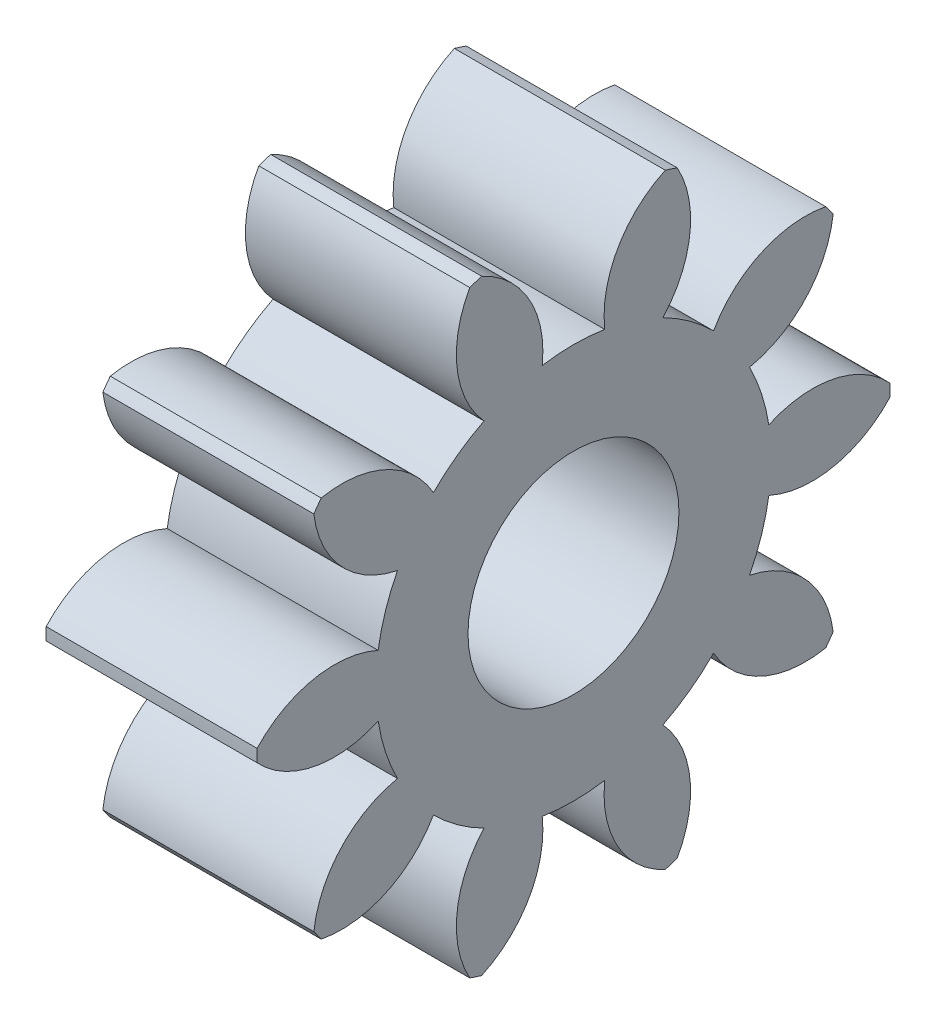
SolidWorks part; units mm, degrees
ref_plane "Plane1" through (0, 0, 0) normal (0, 0, 1) x (1, 0, 0)
ref_plane "Plane2" through (0, 0, 0) normal (0, 1, 0) x (1, 0, 0)
ref_plane "Plane3" through (0, 0, 0) normal (1, 0, 0) x (0, 0, -1)
other "Configuration Table"
sketch "HoldingSke" plane through (0, 0, 0) normal (0, 1, 0) x (1, 0, 0)
  line L0 (0, 0) -> (0.9848, -0.1736)
  line L1 (-15, 0) -> (100, 0) construction
  line L2 (0, 0) -> (-2.1039, 2.3779)
  line L3 (0, 0) -> (-11.863, 4.5341)
  line L4 (0, 0) -> (8.5048, 1.4996)
  line L5 (0, 0) -> (-46.8476, -17.4728)
  line L6 (0, 0) -> (-3.3159, -2.2372)
  line L7 (-2.1039, 2.3779) -> (8.6586, 51.2059)
  line L8 (-76.2, 54.61) -> (-75.5, 54.61)
  line L9 (-71.009, 38.7566) -> (-53.1078, 45.2721)
  line L10 (-76.2, 71.12) -> (104.1128, 71.12)
  line L11 (0, 0) -> (-4, 0)
  line L12 (-76.2, 101.6) -> (-76.162, 101.6)
  line L13 (24.9733, 27.94) -> (52.9518, 28.4284)
  line L14 (24.9733, 27.94) -> (24.9743, 27.94)
  line L15 (24.9733, 27.94) -> (100.4006, 29.5858)
  line L16 (-63.627, -1) -> (-12.827, -1)
  circle A0 centre (0, 0) radius 2
  circle A1 centre (0, 0) radius 3.749
  circle A2 centre (0, 0) radius 37.5
  circle A3 centre (0, 0) radius 2
  dimension "MHD" = 7.498
  dimension "Hub_dia" = 75
  dimension "Bore" = 4
  dimension "MBD" = 4
  dimension "Num_teeth" = 10
  dimension "Pitch" = 1
  dimension "Overall_len" = 50
  dimension "Show_teeth" = 10
  dimension "Thickness" = 4
  dimension "OAL" = 50.0001
  dimension "T_dim" = 0.7
  dimension "Ap" = 20
  dimension "H" = 19.05
  dimension "Pitch_radius" = 180.3128
  dimension "Width" = 4
  dimension "Backlash" = 0.038
  dimension "Addendum_fac" = 1
  dimension "Dedendum_fac" = 1.25
  dimension "Clearance_fac" = 0.25
  dimension "Dedendum_add" = 0.001
  dimension "Module" = 1
sketch "BasProSke" plane through (0, 0, 0) normal (0, 1, 0) x (1, 0, 0)
  line L0 (-10, 0) -> (60, 0) construction
  line L1 (0, 0) -> (0, 6)
  line L2 (0, 0) -> (4, 0)
  line L3 (4, 0) -> (4, 6)
  line L4 (4, 6) -> (0, 6)
  dimension "Thickness" = 4
  dimension "Diameter" = 12
revolve "Base-Revolve" add sketch "BasProSke" angle 360 about L0
sketch "TooCutSke" plane through (0, 0, 0) normal (1, 0, 0) x (0, 0, -1)
  line L1 (0, 0) -> (0, 107) construction
  line L2 (0, 0) -> (-0.8485, 4.9275) construction
  line L3 (0, 0) -> (-3.0584, 9.4126) construction
  line L4 (-0.8485, 4.9275) -> (-1.5292, 4.7063) construction
  arc A0 (0.5928, 3.7018) -> (-0.5928, 3.7018) centre (0, 0) ccw
  arc A1 (1.7758, 5.7578) -> (-1.7758, 5.7578) centre (0, 0) ccw
  circle A2 centre (0, 0) radius 5 construction
  circle A3 centre (0, 0) radius 4.6985 construction
  arc A4 (-0.5928, 3.7018) -> (-1.7758, 5.7578) centre (-2.5801, 3.9267) ccw
  arc A5 (1.7758, 5.7578) -> (0.5928, 3.7018) centre (2.5801, 3.9267) ccw
  dimension "Root_dia" = 7.498
  dimension "Overcut_dia" = 12.0508
  dimension "Pitch_dia" = 10
  dimension "Base_dia" = 9.3969
  dimension "Flank_rad" = 2
  dimension "Half_ang" = 18
  dimension "Half_CT" = 0.7157
extrude "ToothCut" cut sketch "TooCutSke" along normal through all
fillet "Breaks" [suppressed] radius 0.02
fillet "RootFillets" [suppressed] radius 0.251
pattern_circular "TeethCuts" count 10 every 36 about axis through (-10, 0, 0) along (1, 0, 0) of "ToothCut", "RootFillets", "Breaks"
sketch "HubNeaOneSke" plane through (0, 0, 0) normal (-1, 0, 0) x (0, 0, 1)
  circle A0 centre (0, 0) radius 3.749
  dimension "Diameter" = 7.498
extrude "HubNearOne" [suppressed] add sketch "HubNeaOneSke" along normal blind 46.0001
sketch "HubNeaBotSke" plane through (0, 0, 0) normal (-1, 0, 0) x (0, 0, 1)
  circle A0 centre (0, 0) radius 3.749
  dimension "Diameter" = 7.498
extrude "HubNearBoth" [suppressed] add sketch "HubNeaBotSke" along normal blind 23
ref_plane "FarPln" through (4, 0, 0) normal (1, 0, 0) x (0, 0, -1)
sketch "HubFarSke" plane through (4, 0, 0) normal (1, 0, 0) x (0, 0, -1)
  circle A0 centre (0, 0) radius 3.749
  dimension "Diameter" = 7.498
extrude "HubFar" [suppressed] add sketch "HubFarSke" along normal blind 23
sketch "BorSke" plane through (0, 0, 0) normal (1, 0, 0) x (0, 0, -1)
  circle A0 centre (0, 0) radius 2
  dimension "Diameter" = 4
extrude "Bore" cut sketch "BorSke" along normal mid plane 100.0001
sketch "KeySke" plane through (0, 0, 0) normal (1, 0, 0) x (0, 0, -1)
  line L0 (-0.8, 0) -> (-0.8, 2.7)
  line L1 (-0.8, 2.7) -> (0.8, 2.7)
  line L2 (0.8, 2.7) -> (0.8, 0)
  line L3 (0, 0) -> (0, 34) construction
  line L4 (-0.8, 0) -> (0.8, 0)
  dimension "Offset" = 2.7
  dimension "Width" = 1.6
extrude "Keyway" [suppressed] cut sketch "KeySke" along normal mid plane 100.0001
pattern_circular "Keyway2" [suppressed] count 2 every 90 about axis through (-10, 0, 0) along (1, 0, 0)
equation "' \"Module@HoldingSke\" = 6.35"
equation "' \"Num_teeth@HoldingSke\" = 12"
equation "' \"Ap@HoldingSke\" =  20"
equation "' \"Ap@HoldingSke\" = 20"
equation "' \"Width@HoldingSke\" = 0.5 * 25.4"
equation "' \"Hub_dia@HoldingSke\"= 1 * 25.4"
equation "' \"Hub_dia@HoldingSke\" = 1 * 25.4"
equation "' \"Overall_len@HoldingSke\" = 1.0 * 25.4"
equation "' \"Bore@HoldingSke\" = 0.75 * 25.4"
equation "' \"T_dim@HoldingSke\" = 0.1 * 25.4"
equation "' \"Width@KeySke\" = 0.25 * 25.4"
equation "' \"Show_teeth@HoldingSke\" = 13"
equation "' \"Backlash@HoldingSke\" = 0.009 * 25.4"
equation "' \"Addendum_fac@HoldingSke\" = 1.0"
equation "' \"Dedendum_fac@HoldingSke\" = 1.25"
equation "' \"Dedendum_add@HoldingSke\" = 0.00005 * 25.4"
equation "' \"Clearance_fac@HoldingSke\" = 0.25"
equation "\"Pitch@HoldingSke\" = 1 / \"Module@HoldingSke\""
equation "\"Overcut_dia@TooCutSke\" = (\"Num_teeth@HoldingSke\" + 2 * \"Addendum_fac@HoldingSke\") / \"Pitch@HoldingSke\" + 0.002 * 25.4"
equation "\"Pitch_dia@TooCutSke\" = \"Num_teeth@HoldingSke\" / \"Pitch@HoldingSke\""
equation "\"Base_dia@TooCutSke\" = \"Num_teeth@HoldingSke\" / \"Pitch@HoldingSke\" * cos((\"Ap@HoldingSke\"  * 3.14159265 / 180))"
equation "\"Root_dia@TooCutSke\" = (\"Num_teeth@HoldingSke\" + 2) / \"Pitch@HoldingSke\" - 2 * (\"Addendum_fac@HoldingSke\" + \"Dedendum_fac@HoldingSke\") / \"Pitch@HoldingSke\" - \"Dedendum_add@HoldingSke\" * 2"
equation "\"Half_ang@TooCutSke\" = 180 / \"Num_teeth@HoldingSke\""
equation "\"Half_CT@TooCutSke\" = \"Num_teeth@HoldingSke\" / \"Pitch@HoldingSke\" * sin((3.14159265 / 2 / \"Num_teeth@HoldingSke\")) / 2 - 7 * \"Backlash@HoldingSke\" / 4"
equation "\"Flank_rad@TooCutSke\" = \"Num_teeth@HoldingSke\" / \"Pitch@HoldingSke\" / 5"
equation "\"Radius@RootFillets\" = \"Clearance_fac@HoldingSke\" / \"Pitch@HoldingSke\" + \"Dedendum_add@HoldingSke\""
equation "\"Break_rad@Breaks\" = 0.02 / \"Pitch@HoldingSke\""
equation "\"Thickness@HoldingSke\" = \"Width@HoldingSke\""
equation "\"OAL@HoldingSke\" = \"Thickness@HoldingSke\""
equation "\"MHD@HoldingSke\" = (\"Num_teeth@HoldingSke\" + 2) / \"Pitch@HoldingSke\" - 2 * (\"Addendum_fac@HoldingSke\" + \"Dedendum_fac@HoldingSke\")  / \"Pitch@HoldingSke\" - \"Dedendum_add@HoldingSke\" * 2"
equation "\"MBD@HoldingSke\" = (\"Num_teeth@HoldingSke\" + 2) / \"Pitch@HoldingSke\" - 2 * (\"Addendum_fac@HoldingSke\" + \"Dedendum_fac@HoldingSke\")  / \"Pitch@HoldingSke\" - \"Dedendum_add@HoldingSke\" * 2 - 0.002 * 25.4"
equation "\"MHD@HoldingSke\" = ((sgn( \"MHD@HoldingSke\" - \"Hub_dia@HoldingSke\" )-1)*( \"MHD@HoldingSke\" - \"Hub_dia@HoldingSke\" ))/-2+ \"Hub_dia@HoldingSke\""
equation "\"MBD@HoldingSke\" = ((sgn( \"MBD@HoldingSke\" - \"Bore@HoldingSke\" )-1)*( \"MBD@HoldingSke\" - \"Bore@HoldingSke\" ))/-2+ \"Bore@HoldingSke\""
equation "\"OAL@HoldingSke\" = ((sgn( \"OAL@HoldingSke\" - \"Overall_len@HoldingSke\" )+1)*( \"OAL@HoldingSke\" - \"Overall_len@HoldingSke\" ))/2 + \"Overall_len@HoldingSke\" + 0.000002 * 25.4"
equation "\"Num_teeth@TeethCuts\" = int( \"Show_teeth@HoldingSke\" ) + 1"
equation "\"Num_teeth@TeethCuts\" = ((sgn( \"Num_teeth@TeethCuts\" - \"Num_teeth@HoldingSke\" )-1)*( \"Num_teeth@TeethCuts\" - \"Num_teeth@HoldingSke\" ))/-2+ \"Num_teeth@HoldingSke\""
equation "\"Num_teeth@TeethCuts\" = ((sgn( \"Num_teeth@TeethCuts\" - 2.0)+1)*( \"Num_teeth@TeethCuts\" - 2.0))/2 +2.0"
equation "\"Angle@TeethCuts\" = 360.0 / \"Num_teeth@HoldingSke\""
equation "\"Diameter@BasProSke\" = (\"Num_teeth@HoldingSke\" + 2 * \"Addendum_fac@HoldingSke\") / \"Pitch@HoldingSke\""
equation "\"Thickness@BasProSke\"  = \"Thickness@HoldingSke\""
equation "' \"Fillet_rad@BasProSke\" =  \"Thickness@HoldingSke\" * 0.05"
equation "' \"Fillet_rad@BasProSke\" = \"Thickness@HoldingSke\" * 0.05"
equation "\"MHD@HoldingSke\" = ((sgn( \"MHD@HoldingSke\" - \"Root_dia@TooCutSke\" )-1)*( \"MHD@HoldingSke\" - \"Root_dia@TooCutSke\" ))/-2+ \"Root_dia@TooCutSke\""
equation "\"Diameter@HubNeaOneSke\" = \"MHD@HoldingSke\""
equation "\"Length@HubNearOne\" = \"OAL@HoldingSke\" - \"Thickness@BasProSke\""
equation "\"Diameter@HubNeaBotSke\" = \"MHD@HoldingSke\""
equation "\"Length@HubNearBoth\" = ( \"OAL@HoldingSke\" - \"Thickness@BasProSke\" ) / 2.0"
equation "\"Thickness@FarPln\" = \"Thickness@BasProSke\""
equation "\"Diameter@HubFarSke\" = \"MHD@HoldingSke\""
equation "\"Length@HubFar\" = ( \"OAL@HoldingSke\" - \"Thickness@BasProSke\" ) / 2.0"
equation "\"Diameter@BorSke\" = \"MBD@HoldingSke\""
equation "\"D1@Bore\" = \"OAL@HoldingSke\" * 2.0"
equation "\"D1@Keyway\" = \"OAL@HoldingSke\" * 2.0"
equation "\"Offset@KeySke\" = \"T_dim@HoldingSke\" + \"MBD@HoldingSke\" / 2.0"
